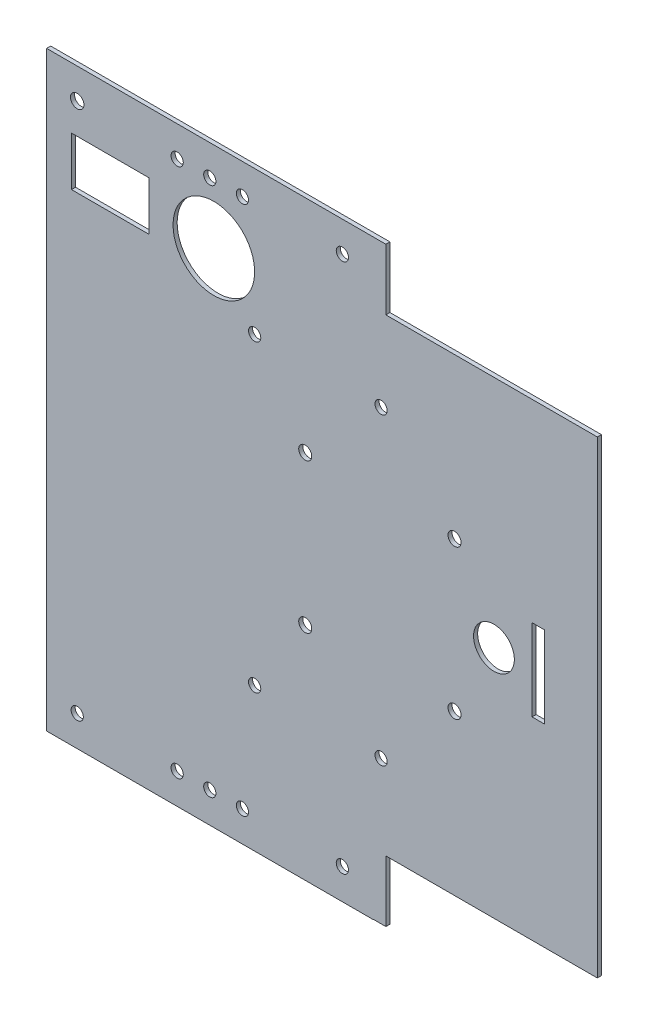
SolidWorks part; units mm, degrees
ref_plane "Front Plane" through (0, 0, 0) normal (0, 0, 1) x (1, 0, 0)
ref_plane "Top Plane" through (0, 0, 0) normal (0, 1, 0) x (1, 0, 0)
ref_plane "Right Plane" through (0, 0, 0) normal (1, 0, 0) x (0, 0, -1)
sketch "Sketch1" plane through (0, 0, 0) normal (0, 0, 1) x (1, 0, 0)
  line L1 (0, 0) -> (-135, 0)
  line L2 (0, 0) -> (0, -115)
  line L3 (0, -115) -> (-135, -115)
  line L4 (-135, 0) -> (-135, -115)
  dimension "D1" = 115
  dimension "D2" = 135
extrude "Boss-Extrude1" add sketch "Sketch1" along normal blind 1
sketch "Sketch3" plane through (0, 0, 0) normal (0, 0, -1) x (-1, 0, 0)
  line L1 (135, -115) -> (120, -115)
  line L2 (135, -115) -> (135, -130)
  line L3 (135, -130) -> (120, -130)
  line L4 (120, -115) -> (120, -130)
  line L5 (135, 0) -> (120, 0)
  line L6 (135, 0) -> (135, 15)
  line L7 (135, 15) -> (120, 15)
  line L8 (120, 0) -> (120, 15)
  dimension "D1" = 15
  dimension "D2" = 15
  dimension "D3" = 15
  dimension "D4" = 15
extrude "Boss-Extrude3" add sketch "Sketch3" against normal blind 1
sketch "Sketch4" plane through (0, 0, 0) normal (0, 0, -1) x (-1, 0, 0)
  line L0 (120, -115) -> (0, -115) construction
  line L1 (70, -115) -> (55, -115)
  line L2 (70, -115) -> (70, -130)
  line L3 (70, -130) -> (55, -130)
  line L4 (55, -115) -> (55, -130)
  line L5 (120, -115) -> (120, -130) construction
  line L6 (0, 0) -> (120, 0) construction
  line L7 (55, 0) -> (70, 0)
  line L8 (55, 0) -> (55, 15)
  line L9 (55, 15) -> (70, 15)
  line L10 (70, 0) -> (70, 15)
  dimension "D1" = 15
  dimension "D2" = 15
  dimension "D3" = 50
  dimension "D4" = 15
  dimension "D5" = 15
extrude "Boss-Extrude4" add sketch "Sketch4" against normal blind 1
sketch "Sketch5" plane through (0, 0, 0) normal (0, 0, -1) x (-1, 0, 0)
  line L0 (55, -115) -> (55, -130) construction
  line L1 (55, -130) -> (70, -130) construction
  line L2 (120, -115) -> (120, -130) construction
  line L3 (120, -130) -> (135, -130) construction
  line L4 (120, 15) -> (120, 0) construction
  line L5 (135, 15) -> (120, 15) construction
  line L6 (55, 15) -> (55, 0) construction
  line L7 (70, 15) -> (55, 15) construction
  circle A0 centre (62.5, -122.5) radius 1.5
  circle A1 centre (127.5, -122.5) radius 1.5
  circle A2 centre (62.5, 7.5) radius 1.5
  circle A3 centre (127.5, 7.5) radius 1.6441
  dimension "D1" = 7.5
  dimension "D2" = 7.5
  dimension "D3" = 7.5
  dimension "D4" = 7.5
  dimension "D5" = 7.5
  dimension "D6" = 7.5
  dimension "D7" = 7.5
  dimension "D8" = 7.5
extrude "Cut-Extrude1" cut sketch "Sketch5" against normal blind 1
sketch "Sketch6" plane through (0, 0, 0) normal (0, 0, -1) x (-1, 0, 0)
  line L1 (120, -115) -> (70, -115)
  line L2 (120, -115) -> (120, -130)
  line L3 (120, -130) -> (70, -130)
  line L4 (70, -115) -> (70, -130)
  line L5 (120, 0) -> (70, 0)
  line L6 (120, 0) -> (120, 15)
  line L7 (120, 15) -> (70, 15)
  line L8 (70, 0) -> (70, 15)
  line L9 (55, -115) -> (0, -115)
  line L10 (55, -115) -> (55, -130)
  line L11 (55, -130) -> (0, -130)
  line L12 (0, -115) -> (0, -130)
  line L13 (55, 0) -> (0, 0)
  line L14 (55, 0) -> (55, 15)
  line L15 (55, 15) -> (0, 15)
  line L16 (0, 0) -> (0, 15)
  line L17 (135, -130) -> (0, -130)
  line L18 (135, -130) -> (135, -150)
  line L19 (135, -150) -> (0, -150)
  line L20 (0, -130) -> (0, -150)
  line L21 (0, 15) -> (135, 15)
  line L22 (0, 15) -> (0, 35)
  line L23 (0, 35) -> (135, 35)
  line L24 (135, 15) -> (135, 35)
  dimension "D1" = 20
  dimension "D2" = 20
extrude "Boss-Extrude5" add sketch "Sketch6" against normal blind 1 from surface contours L2 L1 L4 L3
sketch "Sketch7" plane through (0, 0, 0) normal (0, 0, -1) x (-1, 0, 0)
  line L1 (55, -115) -> (0, -115)
  line L2 (55, -115) -> (55, -129.9314)
  line L3 (55, -129.9314) -> (0, -129.9314)
  line L4 (0, -115) -> (0, -129.9314)
extrude "Boss-Extrude6" add sketch "Sketch7" against normal blind 1
sketch "Sketch8" plane through (0, 0, 0) normal (0, 0, -1) x (-1, 0, 0)
  line L1 (55, 0) -> (0, 0)
  line L2 (55, 0) -> (55, 14.9314)
  line L3 (55, 14.9314) -> (0, 14.9314)
  line L4 (0, 0) -> (0, 14.9314)
extrude "Boss-Extrude10" add sketch "Sketch8" against normal blind 1
sketch "Sketch9" plane through (0, 0, 0) normal (0, 0, -1) x (-1, 0, 0)
  line L1 (70, 0) -> (120, 0)
  line L2 (70, 0) -> (70, 15)
  line L3 (70, 15) -> (120, 15)
  line L4 (120, 0) -> (120, 15)
extrude "Boss-Extrude11" add sketch "Sketch9" against normal blind 1
sketch "Sketch10" plane through (0, 0, 1) normal (0, 0, 1) x (1, 0, 0)
  line L0 (-135, 15) -> (-135, -130) construction
  line L1 (0, 14.9314) -> (-135, 14.9314)
  line L2 (0, 14.9314) -> (0, 34.9314)
  line L3 (0, 34.9314) -> (-135, 34.9314)
  line L4 (-135, 14.9314) -> (-135, 34.9314)
  dimension "D1" = 0
  dimension "D2" = 20
extrude "Boss-Extrude12" add sketch "Sketch10" against normal blind 1
sketch "Sketch12" plane through (0, 0, 0) normal (0, 0, -1) x (-1, 0, 0)
  line L0 (135, 34.9314) -> (135, -130) construction
  line L1 (0, 34.9314) -> (135, 34.9314)
  line L2 (0, 34.9314) -> (0, 14.9314)
  line L3 (0, 14.9314) -> (135, 14.9314)
  line L4 (135, 34.9314) -> (135, 14.9314)
  dimension "D1" = 20
extrude "Cut-Extrude2" cut sketch "Sketch12" against normal blind 1
sketch "Sketch14" plane through (0, 0, 0) normal (0, 0, -1) x (-1, 0, 0)
  line L1 (0, -129.9314) -> (51.8399, -129.9314)
  line L2 (0, -129.9314) -> (0, -114.9314)
  line L3 (0, -114.9314) -> (51.8399, -114.9314)
  line L4 (51.8399, -129.9314) -> (51.8399, -114.9314)
  line L5 (0, 14.9314) -> (51.8399, 14.9314)
  line L6 (0, 14.9314) -> (0, -0.0686)
  line L7 (0, -0.0686) -> (51.8399, -0.0686)
  line L8 (51.8399, 14.9314) -> (51.8399, -0.0686)
  dimension "D1" = 15
  dimension "D2" = 15
extrude "Cut-Extrude3" cut sketch "Sketch14" against normal blind 1
sketch "Sketch15" plane through (0, 0, 0) normal (0, 0, -1) x (-1, 0, 0)
  line L0 (0, -0.0686) -> (51.8399, -0.0686) construction
  line L2 (55, -130) -> (135, -130) construction
  line L3 (135, 14.9314) -> (135, -130) construction
  line L4 (51.8399, 14.9314) -> (135, 14.9314) construction
  line L5 (0, -114.9314) -> (0, -0.0686) construction
  line L6 (51.8399, -114.9314) -> (0, -114.9314) construction
  circle A0 centre (71.8399, -125) radius 1.5
  circle A3 centre (113.4634, -125) radius 1.5
  circle A4 centre (100, -125) radius 1.5
  circle A5 centre (87, -125) radius 1.5
  circle A6 centre (100, 9.9314) radius 1.5
  circle A7 centre (87, 9.9314) radius 1.5
  circle A8 centre (32.9965, -109.9314) radius 1.5
  circle A9 centre (20, -109.6312) radius 1.5
  circle A10 centre (32.9965, -5.0686) radius 1.5
  circle A11 centre (20, -5.0686) radius 1.5
  dimension "D1" = 5
  dimension "D5" = 5
  dimension "D8" = 13
  dimension "D12" = 5
  dimension "D2" = 5
  dimension "D3" = 13
  dimension "D4" = 35
  dimension "D6" = 5
  dimension "D7" = 35
  dimension "D9" = 20
  dimension "D10" = 5
  dimension "D11" = 5.3003
  dimension "D13" = 5
extrude "Cut-Extrude5" cut sketch "Sketch15" against normal blind 10
sketch "Sketch16" plane through (0, 0, 0) normal (0, 0, -1) x (-1, 0, 0)
  line L0 (135, 14.9314) -> (135, -130) construction
  line L1 (55, -130) -> (135, -130) construction
  line L2 (51.8399, 14.9314) -> (135, 14.9314) construction
  circle A0 centre (130, -95) radius 1.5
  circle A1 centre (130, -82) radius 1.5
  circle A2 centre (130, -33.0686) radius 1.5
  circle A3 centre (130, -20.0686) radius 1.5
  dimension "D1" = 5
  dimension "D2" = 5
  dimension "D3" = 5
  dimension "D4" = 5
  dimension "D5" = 13
  dimension "D6" = 13
  dimension "D7" = 35
  dimension "D8" = 35
extrude "Cut-Extrude6" cut sketch "Sketch16" against normal blind 10
sketch "Sketch17" plane through (0, 0, 0) normal (0, 0, -1) x (-1, 0, 0)
  line L0 (0, -114.9314) -> (0, -0.0686) construction
  line L1 (51.8399, -114.9314) -> (0, -114.9314) construction
  line L2 (0, -0.0686) -> (51.8399, -0.0686) construction
  circle A0 centre (35, -75.8014) radius 1.6
  circle A1 centre (35, -39.2014) radius 1.6
  circle A2 centre (71.6, -39.2014) radius 1.6
  circle A3 centre (71.6, -75.8014) radius 1.6
  dimension "D1" = 36.6
  dimension "D5" = 36.6
  dimension "D2" = 36.6
  dimension "D3" = 35
  dimension "D4" = 35
  dimension "D6" = 36.6
  dimension "D7" = 0
  dimension "D8" = 39.13
  dimension "D9" = 39.1329
extrude "Cut-Extrude9" cut sketch "Sketch17" against normal blind 1
sketch "Sketch18" plane through (0, 0, 0) normal (0, 0, -1) x (-1, 0, 0)
  line L0 (51.8399, 14.9314) -> (135, 14.9314) construction
  line L1 (55, -130) -> (135, -130) construction
  line L2 (135, 14.9314) -> (135, -130) construction
  line L3 (0, -114.9314) -> (0, -0.0686) construction
  circle A0 centre (115, -20.2686) radius 1.5
  circle A1 centre (115, -94.8) radius 1.5
  circle A2 centre (84, -20.2686) radius 1.5
  circle A3 centre (84, -94.8) radius 1.5
  circle A4 centre (95, -107.0489) radius 10
  dimension "D1" = 31
  dimension "D9" = 95
  dimension "D2" = 31
  dimension "D3" = 74.5314
  dimension "D4" = 20
  dimension "D5" = 35.2
  dimension "D6" = 35.2
  dimension "D7" = 0
  dimension "D8" = 20
extrude "Cut-Extrude10" cut sketch "Sketch18" against normal blind 10
sketch "Sketch19" plane through (0, 0, 0) normal (0, 0, -1) x (-1, 0, 0)
  line L0 (0, -114.9314) -> (0, -0.0686) construction
  circle A0 centre (94, -7.0489) radius 10
  circle A1 centre (95, -107.0489) radius 10 construction
  dimension "D1" = 94
  dimension "D2" = 100
extrude "Cut-Extrude11" cut sketch "Sketch19" against normal blind 10
sketch "Sketch20" plane through (0, 0, 0) normal (0, 0, -1) x (-1, 0, 0)
  line L1 (109.8994, 0) -> (128.8994, 0)
  line L2 (109.8994, 0) -> (109.8994, -12)
  line L3 (109.8994, -12) -> (128.8994, -12)
  line L4 (128.8994, 0) -> (128.8994, -12)
  dimension "D1" = 19
  dimension "D2" = 12
extrude "Cut-Extrude12" cut sketch "Sketch20" against normal blind 10
sketch "Sketch21" plane through (0, 0, 0) normal (0, 0, -1) x (-1, 0, 0)
  line L0 (0, -0.0686) -> (51.8399, -0.0686) construction
  line L1 (15, -47.4986) -> (16, -47.4986)
  line L2 (15, -47.4986) -> (15, -67.4986)
  line L3 (15, -67.4986) -> (16, -67.4986)
  line L4 (16, -47.4986) -> (16, -67.4986)
  line L5 (51.8399, -114.9314) -> (0, -114.9314) construction
  line L6 (0, -114.9314) -> (0, -0.0686) construction
  circle A0 centre (25.3354, -57.4963) radius 5
  point P10 (0, -57.5)
  dimension "D1" = 1
  dimension "D2" = 20
  dimension "D3" = 47.43
  dimension "D4" = 47.4329
  dimension "D5" = 15
extrude "Cut-Extrude13" cut sketch "Sketch21" against normal blind 10
sketch "Sketch22" plane through (0, 0, 0) normal (0, 0, -1) x (-1, 0, 0)
  circle A0 centre (53, -20.2686) radius 1.5
  circle A1 centre (53, -94.8) radius 1.5
  circle A2 centre (84, -20.2686) radius 1.5 construction
  circle A3 centre (84, -94.8) radius 1.5 construction
  dimension "D1" = 0
  dimension "D2" = 0
  dimension "D3" = 31
  dimension "D4" = 31
extrude "Cut-Extrude14" cut sketch "Sketch22" against normal blind 10
sketch "Sketch23" plane through (0, 0, 0) normal (0, 0, -1) x (-1, 0, 0)
  circle A0 centre (19.9112, -5.1546) radius 1.6236
  circle A1 centre (32.9965, -5.0686) radius 1.5
  circle A2 centre (100, 9.9314) radius 1.5
  circle A3 centre (86.9577, 9.9314) radius 1.4577
  circle A4 centre (95, -107.0489) radius 10
  circle A5 centre (20, -109.6312) radius 1.5
  circle A6 centre (32.9965, -109.9314) radius 1.5
  circle A7 centre (87, -125) radius 1.5
  circle A8 centre (71.8399, -125) radius 2.6332
  circle A9 centre (100, -125) radius 1.5
  circle A10 centre (113.4634, -125) radius 1.5
  circle A11 centre (130, -20.0686) radius 1.5
  circle A12 centre (130, -33.0686) radius 1.5
  circle A13 centre (130, -82) radius 1.5
  circle A14 centre (130, -95) radius 1.5
  circle A15 centre (115, -20.2686) radius 1.5
  circle A16 centre (115, -94.8) radius 1.5
extrude "Boss-Extrude14" add sketch "Sketch23" against normal blind 1
sketch "Sketch24" plane through (0, 0, 0) normal (0, 0, -1) x (-1, 0, 0)
  circle A0 centre (86.9894, 9.8214) radius 1.8913
extrude "Boss-Extrude15" add sketch "Sketch24" against normal blind 1
sketch "Sketch25" plane through (0, 0, 0) normal (0, 0, -1) x (-1, 0, 0)
  line L1 (15, -67.4986) -> (13, -67.4986)
  line L2 (15, -67.4986) -> (15, -47.4971)
  line L3 (15, -47.4971) -> (13, -47.4971)
  line L4 (13, -67.4986) -> (13, -47.4971)
  dimension "D1" = 2
extrude "Cut-Extrude15" cut sketch "Sketch25" against normal blind 1
sketch "Sketch26" plane through (0, 0, 0) normal (0, 0, -1) x (-1, 0, 0)
  line L0 (51.8399, 14.9314) -> (135, 14.9314) construction
  line L1 (55, -130) -> (135, -130) construction
  circle A0 centre (103, 7.4314) radius 1.5
  circle A1 centre (95, 7.4314) radius 1.5
  circle A2 centre (87, 7.4314) radius 1.5
  circle A3 centre (127.5, 7.5) radius 1.6441 construction
  circle A6 centre (103, -122.5) radius 1.5
  circle A7 centre (95, -122.5) radius 1.5
  circle A8 centre (87, -122.5) radius 1.5
  dimension "D1" = 8
  dimension "D5" = 7.5
  dimension "D2" = 8
  dimension "D3" = 7.5
  dimension "D4" = 32.5
  dimension "D6" = 7.5
  dimension "D7" = 7.5
extrude "Cut-Extrude16" cut sketch "Sketch26" against normal blind 1
